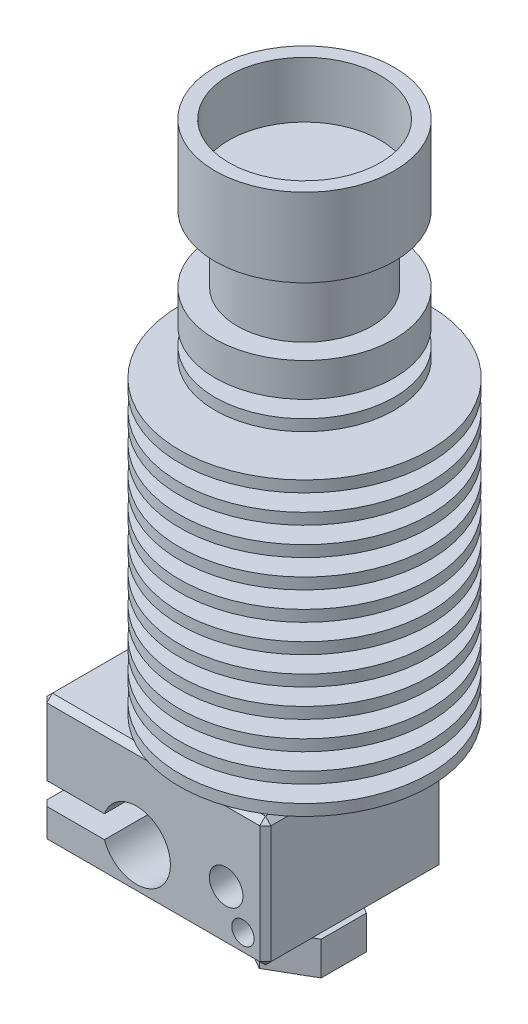
SolidWorks part; units mm, degrees
ref_plane "Front Plane" through (0, 0, 0) normal (0, 0, 1) x (1, 0, 0)
ref_plane "Top Plane" through (0, 0, 0) normal (0, 1, 0) x (1, 0, 0)
ref_plane "Right Plane" through (0, 0, 0) normal (1, 0, 0) x (0, 0, -1)
ref_plane "Plane1" through (0, -42.25, 0) normal (0, -1, 0) x (1, 0, 0)
sketch "Sketch1" plane through (0, -42.25, 0) normal (0, -1, 0) x (1, 0, 0)
  line L0 (-3.5, 2.0207) -> (-3.5, -2.0207)
  line L1 (-3.5, -2.0207) -> (0, -4.0415)
  line L2 (0, -4.0415) -> (3.5, -2.0207)
  line L3 (3.5, -2.0207) -> (3.5, 2.0207)
  line L4 (3.5, 2.0207) -> (0, 4.0415)
  line L5 (0, 4.0415) -> (-3.5, 2.0207)
extrude "Boss-Extrude1" add sketch "Sketch1" against normal blind 3
sketch "Sketch2" plane through (0, -39.25, 0) normal (0, 1, 0) x (-1, 0, 0)
  circle A0 centre (0, 0) radius 2.5
extrude "Boss-Extrude2" add sketch "Sketch2" along normal blind 1
ref_plane "Plane2" through (0, -38.25, 0) normal (0, -1, 0) x (1, 0, 0)
sketch "Sketch3" plane through (0, -38.25, 0) normal (0, -1, 0) x (1, 0, 0)
  line L0 (-15.5, -8) -> (4.5, -8)
  line L1 (4.5, -8) -> (4.5, 8)
  line L2 (4.5, 8) -> (-15.5, 8)
  line L3 (-15.5, 8) -> (-15.5, -8)
extrude "Boss-Extrude3" add sketch "Sketch3" against normal blind 11.5
sketch "Sketch4" plane through (0, 0, -8) normal (0, 0, -1) x (-1, 0, 0)
  line L0 (15.5, -33.25) -> (9.8549, -33.25)
  line L1 (9.8549, -35.25) -> (15.5, -35.25)
  line L2 (15.5, -35.25) -> (15.5, -33.25)
  arc A0 (9.8549, -33.25) -> (9.8549, -35.25) centre (7, -34.25) cw
extrude "Cut-Extrude1" cut sketch "Sketch4" against normal through all
ref_plane "Plane3" through (0, -34.25, 0) normal (0, -1, 0) x (1, 0, 0)
sketch "Sketch5" plane through (0, -34.25, 0) normal (0, -1, 0) x (1, 0, 0)
  line L0 (-3.975, 8) -> (-7, 8)
  line L1 (-7, 8) -> (-7, -8)
  line L2 (-7, -8) -> (-3.975, -8)
  line L3 (-3.975, -8) -> (-3.975, 8)
  line L4 (-7, 8) -> (-7, -8) construction
revolve "Cut-Revolve1" cut sketch "Sketch5" angle 360 about L4
sketch "Sketch6" plane through (0, 0, 0) normal (0, 0, 1) x (1, 0, 0)
  line L0 (1.9, -42.25) -> (0, -42.25)
  line L1 (0, -42.25) -> (0, -44.25)
  line L2 (0, -44.25) -> (0.5, -44.25)
  line L3 (0.5, -44.25) -> (1.9, -42.25)
  line L4 (0, -42.25) -> (0, -44.25) construction
revolve "Revolve1" add sketch "Sketch6" angle 360 about L4
sketch "Sketch7" plane through (0, 0, 0) normal (0, 0, 1) x (1, 0, 0)
  line L0 (8, 21.35) -> (0, 21.35)
  line L1 (0, 21.35) -> (0, -26.75)
  line L2 (0, -26.75) -> (2, -26.75)
  line L3 (2, -26.75) -> (2, -24.65)
  line L4 (2, -24.65) -> (11.15, -24.65)
  line L5 (11.15, -24.65) -> (11.15, -23.65)
  line L6 (11.15, -23.65) -> (7, -23.65)
  line L7 (7, -23.65) -> (7, -22.15)
  line L8 (7, -22.15) -> (11.15, -22.15)
  line L9 (11.15, -22.15) -> (11.15, -21.15)
  line L10 (11.15, -21.15) -> (6.75, -21.15)
  line L11 (6.75, -21.15) -> (6.75, -19.65)
  line L12 (6.75, -19.65) -> (11.15, -19.65)
  line L13 (11.15, -19.65) -> (11.15, -18.65)
  line L14 (11.15, -18.65) -> (6.5, -18.65)
  line L15 (6.5, -18.65) -> (6.5, -17.15)
  line L16 (6.5, -17.15) -> (11.15, -17.15)
  line L17 (11.15, -17.15) -> (11.15, -16.15)
  line L18 (11.15, -16.15) -> (6.25, -16.15)
  line L19 (6.25, -16.15) -> (6.25, -14.65)
  line L20 (6.25, -14.65) -> (11.15, -14.65)
  line L21 (11.15, -14.65) -> (11.15, -13.65)
  line L22 (11.15, -13.65) -> (6, -13.65)
  line L23 (6, -13.65) -> (6, -12.15)
  line L24 (6, -12.15) -> (11.15, -12.15)
  line L25 (11.15, -12.15) -> (11.15, -11.15)
  line L26 (11.15, -11.15) -> (5.75, -11.15)
  line L27 (5.75, -11.15) -> (5.75, -9.65)
  line L28 (5.75, -9.65) -> (11.15, -9.65)
  line L29 (11.15, -9.65) -> (11.15, -8.65)
  line L30 (11.15, -8.65) -> (5.5, -8.65)
  line L31 (5.5, -8.65) -> (5.5, -7.15)
  line L32 (5.5, -7.15) -> (11.15, -7.15)
  line L33 (11.15, -7.15) -> (11.15, -6.15)
  line L34 (11.15, -6.15) -> (5.25, -6.15)
  line L35 (5.25, -6.15) -> (5.25, -4.65)
  line L36 (5.25, -4.65) -> (11.15, -4.65)
  line L37 (11.15, -4.65) -> (11.15, -3.65)
  line L38 (11.15, -3.65) -> (5, -3.65)
  line L39 (5, -3.65) -> (5, -2.15)
  line L40 (5, -2.15) -> (11.15, -2.15)
  line L41 (11.15, -2.15) -> (11.15, -1.15)
  line L42 (11.15, -1.15) -> (4.75, -1.15)
  line L43 (4.75, -1.15) -> (4.75, 0.35)
  line L44 (4.75, 0.35) -> (11.15, 0.35)
  line L45 (11.15, 0.35) -> (11.15, 1.35)
  line L46 (11.15, 1.35) -> (4.5, 1.35)
  line L47 (4.5, 1.35) -> (4.5, 2.85)
  line L48 (4.5, 2.85) -> (8, 2.85)
  line L49 (8, 2.85) -> (8, 3.85)
  line L50 (8, 3.85) -> (4.5, 3.85)
  line L51 (4.5, 3.85) -> (4.5, 5.35)
  line L52 (4.5, 5.35) -> (8, 5.35)
  line L53 (8, 5.35) -> (8, 8.35)
  line L54 (8, 8.35) -> (6, 8.35)
  line L55 (6, 8.35) -> (6, 14.35)
  line L56 (6, 14.35) -> (8, 14.35)
  line L57 (8, 14.35) -> (8, 21.35)
  line L58 (0, 21.35) -> (0, -26.75) construction
revolve "Revolve2" add sketch "Sketch7" angle 360 about L58
hole_wizard "Ø3.0 (3) Diameter Hole1" positions "Sketch9" profile "Sketch8" hole size "Ø3.0" standard "ANSI Metric"
sketch "Sketch9" plane through (0, -33.25, 0) normal (0, -1, 0) x (-1, 0, 0)
  point P0 (13, 0)
sketch "Sketch8" plane through (-13, -33.25, 0) normal (1, 0, 0) x (0, 0, -1)
  line L0 (0, 0) -> (0, 54.6)
  line L1 (0, 54.6) -> (1.5, 54.6)
  line L2 (1.5, 54.6) -> (1.5, 0)
  line L5 (1.5, 0) -> (0, 0)
  line L11 (0, -6.35) -> (0, 107.95) construction
  dimension "Thru Hole Dia." = 3
  dimension "Thru Hole Depth" = 54.6
hole_wizard "Ø3.0 (3) Diameter Hole2" positions "Sketch11" profile "Sketch10" hole size "Ø3.0" standard "ANSI Metric"
sketch "Sketch11" plane through (0, 0, 8) normal (0, 0, 1) x (1, 0, 0)
  point P0 (1, -33.45)
sketch "Sketch10" plane through (1, -33.45, 8) normal (1, 0, 0) x (0, -1, 0)
  line L0 (0, 0) -> (0, 3.45)
  line L1 (0, 3.45) -> (1.5, 3.45)
  line L2 (1.5, 3.45) -> (1.5, 0)
  line L5 (1.5, 0) -> (0, 0)
  line L10 (0, 3.45) -> (-1.5, 3.45) construction
  line L11 (0, -6.35) -> (0, 107.95) construction
  dimension "Hole Dia." = 3
  dimension "Hole Depth" = 3.45
  dimension "Drill Angle" = 180
hole_wizard "Ø3.0 (3) Diameter Hole3" positions "Sketch13" profile "Sketch12" hole size "Ø3.0" standard "ANSI Metric"
sketch "Sketch13" plane through (0, -38.25, 0) normal (0, -1, 0) x (-1, 0, 0)
  point P0 (13, 0)
sketch "Sketch12" plane through (-13, -38.25, 0) normal (1, 0, 0) x (0, 0, -1)
  line L0 (0, 0) -> (0, 59.6)
  line L1 (0, 59.6) -> (1.5, 59.6)
  line L2 (1.5, 59.6) -> (1.5, 0)
  line L5 (1.5, 0) -> (0, 0)
  line L11 (0, -6.35) -> (0, 107.95) construction
  dimension "Thru Hole Dia." = 3
  dimension "Thru Hole Depth" = 59.6
hole_wizard "M2x0.4 Tapped Hole1" positions "Sketch15" profile "Sketch14" tap size "M2x0.4" standard "ANSI Metric"
sketch "Sketch15" plane through (0, 0, 8) normal (0, 0, 1) x (1, 0, 0)
  point P0 (2.5, -36.25)
sketch "Sketch14" plane through (2.5, -36.25, 8) normal (1, 0, 0) x (0, -1, 0)
  line L0 (0, 0) -> (0, 4.45)
  line L1 (0, 4.45) -> (0.775, 4.45)
  line L2 (0.775, 4.45) -> (0.775, 2)
  line L3 (0.775, 2) -> (1, 2)
  line L4 (1, 2) -> (1, 0)
  line L5 (1, 0) -> (0, 0)
  line L10 (0, 4.45) -> (-0.775, 4.45) construction
  line L11 (0, -6.35) -> (0, 107.95) construction
  dimension "Tap Drill Dia." = 1.55
  dimension "Tap Drill Depth" = 4.45
  dimension "Thread Major Dia." = 2
  dimension "Thread Depth" = 2
  dimension "Drill Angle" = 180
hole_wizard "Ø0.4 (0.4) Diameter Hole1" positions "Sketch17" profile "Sketch16" hole size "Ø0.4" standard "ANSI Metric"
sketch "Sketch17" plane through (0, -44.25, 0) normal (0, -1, 0) x (-1, 0, 0)
  point P0 (0, 0)
sketch "Sketch16" plane through (0, -44.25, 0) normal (1, 0, 0) x (0, 0, -1)
  line L0 (0, 0) -> (0, 3)
  line L1 (0, 3) -> (0.2, 3)
  line L2 (0.2, 3) -> (0.2, 0)
  line L5 (0.2, 0) -> (0, 0)
  line L10 (0, 3) -> (-0.2, 3) construction
  line L11 (0, -6.35) -> (0, 107.95) construction
  dimension "Hole Dia." = 0.4
  dimension "Hole Depth" = 3
  dimension "Drill Angle" = 180
hole_wizard "Ø13.5 (13.5) Diameter Hole1" positions "Sketch19" profile "Sketch18" hole size "Ø13.5" standard "ANSI Metric"
sketch "Sketch19" plane through (0, 21.35, 0) normal (0, 1, 0) x (1, 0, 0)
  point P0 (0, 0)
sketch "Sketch18" plane through (0, 21.35, 0) normal (1, 0, 0) x (0, 0, 1)
  line L0 (0, 0) -> (0, 5)
  line L1 (0, 5) -> (6.75, 5)
  line L2 (6.75, 5) -> (6.75, 0)
  line L5 (6.75, 0) -> (0, 0)
  line L10 (0, 5) -> (-6.75, 5) construction
  line L11 (0, -6.35) -> (0, 107.95) construction
  dimension "Hole Dia." = 13.5
  dimension "Hole Depth" = 5
  dimension "Drill Angle" = 180
chamfer "Chamfer1" distance 0.5 angle 45 14 edges at (-15.5, -36.75, 8) (-15.5, -36.75, -8) (-15.5, -38.25, 0) (-5.5, -38.25, 8) (-15.5, -30, -8) (4.5, -38.25, 0) (4.5, -32.5, 8) (-5.5, -38.25, -8) (-15.5, -30, 8) (-15.5, -26.75, 0) (-5.5, -26.75, -8) (4.5, -32.5, -8) (-5.5, -26.75, 8) (4.5, -26.75, 0)
